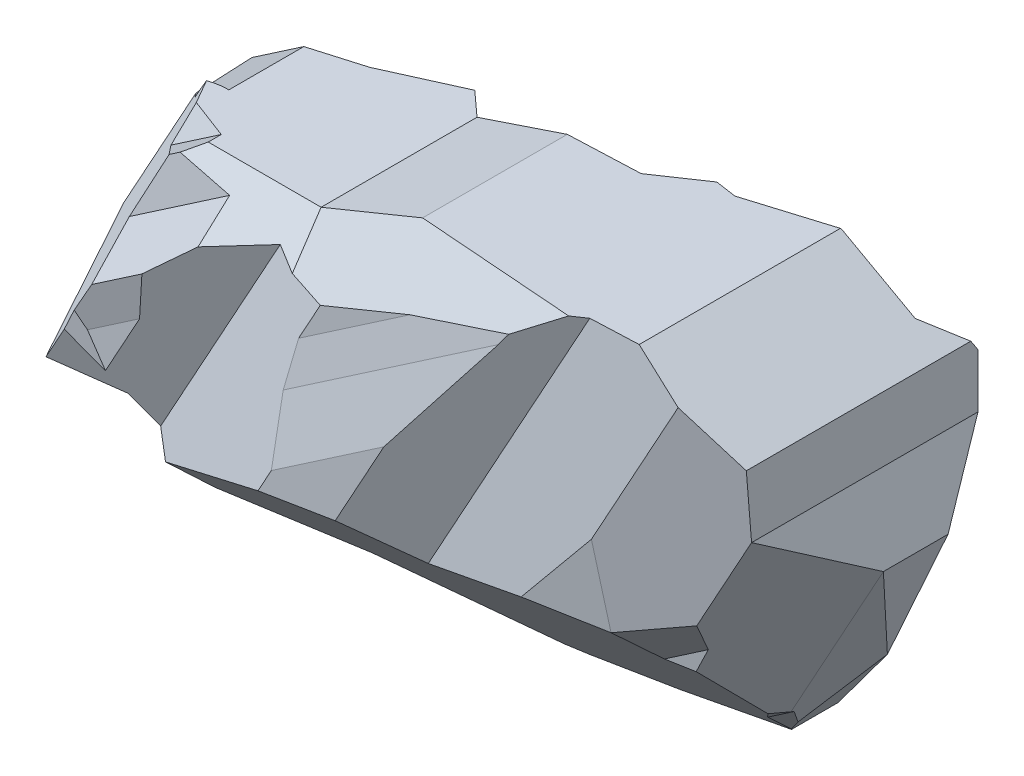
SolidWorks part; units mm, degrees
ref_plane "Front Plane" through (0, 0, 0) normal (0, 0, 1) x (1, 0, 0)
ref_plane "Top Plane" through (0, 0, 0) normal (0, 1, 0) x (1, 0, 0)
ref_plane "Right Plane" through (0, 0, 0) normal (1, 0, 0) x (0, 0, -1)
sketch "Sketch1" plane through (0, 0, 0) normal (0, 0, 1) x (1, 0, 0)
  line L0 (55, 0) -> (-55, 0) construction
  ellipse E0 centre (0, 0) end of major axis (51.6588, 0) minor radius 26.3293 (-36.2676, 18.7496) -> (1.8121, -26.3131) ccw
  spline S0 degree 3 poles (0, 26.3293) (15.0168, 25.039) (45.2457, 18.1207) (16.514, -27.2402) (0, -26.3293) knots 0 0 0 0 0.367873 1 1 1 1
  spline S1 degree 2 poles (0, 26.3293) (-15.7865, 14.5964) (-36.2676, 18.7496) knots 0 0 0 1 1 1
extrude "Boss-Extrude1" add sketch "Sketch1" along normal blind 28.956 contours S0 E0
sketch "Sketch2" plane through (0, 0, 28.956) normal (0, 0, 1) x (1, 0, 0)
  line L0 (-45.695, 8.9128) -> (-42.6216, 12.7546)
  line L1 (-42.6216, 12.7546) -> (-31.2501, 12.7546)
  line L2 (-31.2501, 12.7546) -> (-23.2593, 12.7546)
  line L3 (-23.2593, 12.7546) -> (-13.1171, 16.9036)
  line L4 (-13.1171, 16.9036) -> (0, 19.055)
  line L5 (0, -15.9258) -> (0, 15.9258) construction
  line L6 (0, 19.055) -> (12.936, 21.1767)
  line L7 (12.936, 21.1767) -> (20.6902, 16.9036)
  line L8 (20.6902, 16.9036) -> (23.4327, 15.3924)
  line L9 (23.4327, 8.9128) -> (26.0724, 2.4602)
  line L10 (26.0724, 2.4602) -> (22.0615, -8.9128)
  line L11 (22.0615, -8.9128) -> (15.2146, -17.4713)
  line L12 (15.2146, -17.4713) -> (2.4732, -21.2058)
  line L13 (2.4732, -21.2058) -> (-6.5585, -22.6872)
  line L14 (-6.5585, -22.6872) -> (-8.7604, -22.6872)
  line L15 (-19.8853, -16.3406) -> (-33.4014, -16.3406)
  line L16 (-33.4014, -16.3406) -> (-38.4725, -8.9128)
  line L17 (-38.4725, -8.9128) -> (-44.1583, -6.9076)
  line L18 (-51.52, -1.9292) -> (-45.695, 8.9128)
  line L19 (23.4327, 15.3924) -> (23.4327, 8.9128)
  line L20 (-19.8853, -16.3406) -> (-8.7604, -22.6872)
  line L21 (-51.52, -1.9292) -> (-44.1583, -6.9076)
  ellipse E0 centre (0, 0) end of major axis (51.6588, 0) minor radius 26.3293 (-36.2676, 18.7496) -> (1.8121, -26.3131) ccw construction
extrude "Cut-Extrude1" cut sketch "Sketch2" against normal blind 28.956 flip side to cut
chamfer "Chamfer1" distance 17.78 angle 45 1 edges at (-2.0427, -21.9465, 28.956)
chamfer "Chamfer2" distance 7.62 angle 45 1 edges at (-18.1882, 14.8291, 28.956)
chamfer "Chamfer3" distance 7.62 angle 45 1 edges at (-22.8779, 12.7546, 28.956)
sketch "Sketch3" plane through (11.9646, 21.712, 0) normal (0.4826, 0.8758, 0) x (0.8758, -0.4826, 0)
  line L0 (-41.8262, -14.7446) -> (-38.4979, -21.336)
  line L1 (-43.4848, -21.336) -> (-26.5268, -21.336) construction
  line L2 (-38.4979, -21.336) -> (-35.0058, -28.2517)
  line L3 (-35.0058, -28.2517) -> (-26.5268, -23.9702)
  line L4 (-26.5268, -23.9702) -> (-15.9677, -28.2517)
  line L5 (-15.9677, -28.2517) -> (-9.8231, -28.2517)
  line L6 (-9.8231, -28.2517) -> (-3.4067, -25.0118)
  line L7 (-3.4067, -25.0118) -> (6.5625, -26.6317)
  line L8 (6.5625, -26.6317) -> (16.2213, -25.0118)
  line L9 (16.2213, 0) -> (16.2213, -28.956) construction
  line L10 (16.2213, -25.0118) -> (21.6474, -14.478)
  line L11 (21.6474, 0) -> (21.6474, -28.956) construction
  line L12 (21.6474, -14.478) -> (23.6236, -10.0683)
  line L13 (23.6236, 0) -> (23.6236, -20.1366) construction
  line L14 (23.6236, -10.0683) -> (16.2213, -2.3845)
  line L15 (16.2213, -2.3845) -> (-1.8296, -2.3845)
  line L16 (-1.8296, -2.3845) -> (-12.8954, -7.9722)
  line L17 (-12.8954, -7.9722) -> (-26.5268, -5.7571)
  line L18 (-26.5268, 0) -> (-26.5268, -21.336) construction
  line L19 (-26.5268, -5.7571) -> (-32.073, 0)
  line L20 (-24.1251, 0) -> (24.1251, 0) construction
  line L21 (-32.073, 0) -> (-38.4364, -6.799)
  line L22 (-38.4364, -6.799) -> (-43.4848, -6.799)
  line L23 (-43.4848, -6.799) -> (-42.3267, -7.8828)
  line L24 (-42.3267, -7.8828) -> (-41.8262, -14.7446)
  line L25 (-43.4848, 0) -> (-43.4848, -21.336) construction
extrude "Cut-Extrude2" cut sketch "Sketch3" against normal blind 60.198 flip side to cut
sketch "Sketch4" plane through (-30.3918, -20.749, 0) normal (-0.8259, -0.5638, 0) x (0, 0, 1)
  line L0 (17.379, 33.9403) -> (20.0338, 30.0113)
  line L1 (20.0338, 30.0113) -> (22.4762, 30.0113)
  line L2 (22.4762, 30.0113) -> (23.1085, 26.3409)
  line L3 (23.1085, 26.3409) -> (27.1485, 23.1089)
  line L4 (27.1485, 23.1089) -> (26.4207, 19.7437)
  line L5 (27.5878, 19.1935) -> (14.7446, 25.2479) construction
  line L6 (26.4207, 19.7437) -> (26.4207, 15.9551)
  line L7 (25.4178, 14.3315) -> (28.2517, 18.9194) construction
  line L8 (26.4207, 15.9551) -> (26.992, 12.6387)
  line L9 (26.992, 12.6387) -> (28.2517, 7.3928)
  line L10 (28.2517, 6.1466) -> (28.2517, 15.1612) construction
  line L11 (28.2517, 7.3928) -> (29.398, 2.6189)
  line L12 (29.398, 2.6189) -> (28.8249, -0.0311)
  line L13 (28.8249, -0.0311) -> (26.6317, -2.7726)
  line L14 (26.6317, -6.8982) -> (26.6317, 5.3288) construction
  line L15 (26.6317, -2.7726) -> (25.8217, -9.96)
  line L16 (25.0118, -13.0217) -> (26.6317, -6.8982) construction
  line L17 (25.8217, -9.96) -> (23.1085, -13.3516)
  line L18 (23.1085, -13.3516) -> (22.5757, -18.0793)
  line L19 (22.5757, -18.0793) -> (14.2571, -21.3848)
  line L20 (14.2571, -21.3848) -> (11.527, -24.7974)
  line L21 (11.527, -24.7974) -> (2.1424, -22.7676)
  line L22 (2.1424, -22.7676) -> (4.3525, -18.0793)
  line L23 (4.3525, -18.0793) -> (2.3845, -14.4182)
  line L24 (2.3845, -13.7974) -> (2.3845, -15.0389) construction
  line L25 (2.3845, -14.4182) -> (2.3845, -11.5018)
  line L26 (2.3845, -9.2061) -> (2.3845, -13.7974) construction
  line L27 (2.3845, -1.4019) -> (5.6011, 2.6189)
  line L28 (5.6011, 2.6189) -> (5.6011, 10.0157)
  line L29 (5.6011, 10.0157) -> (6.5345, 14.3315)
  line L30 (2.7814, 14.3315) -> (25.4178, 14.3315) construction
  line L31 (6.5345, 14.3315) -> (3.9928, 18.0933)
  line L32 (3.9928, 18.0933) -> (1.9998, 23.1089)
  line L33 (1.9998, 23.1089) -> (5.2637, 27.1888)
  line L34 (5.2637, 27.1888) -> (6.799, 29.108)
  line L35 (6.799, 22.0832) -> (6.799, 31.3156) construction
  line L36 (8.2934, 31.9758) -> (15.7862, 31.9758)
  line L37 (6.799, 29.108) -> (8.2934, 31.9758)
  line L38 (2.3845, -1.4019) -> (2.3845, -11.5018)
  arc A0 (15.7862, 31.9758) -> (17.379, 33.9403) centre (17.7941, 31.9758) cw
extrude "Cut-Extrude3" cut sketch "Sketch4" against normal blind 65.532 flip side to cut contours L19 L20 L21 L22 L23 L25 L38 L27 L28 L29 L31 L32 L33 L34 L37 L36 A0 L0 L1 L2 L3 L4 L6 L8 L9 L11 L12 L13 L15 L17 L18
